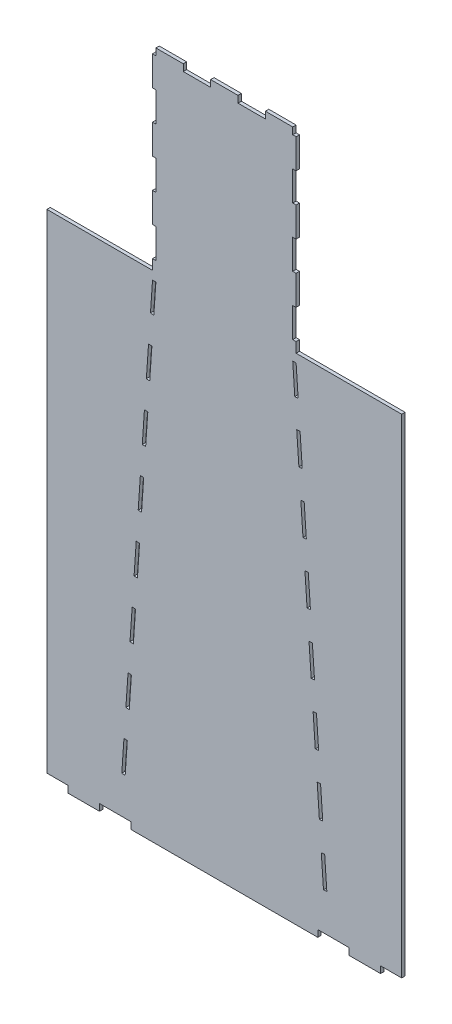
SolidWorks part; units mm, degrees
material "A-Glass Fiber"
ref_plane "Front Plane" through (0, 0, 0) normal (0, 0, 1) x (1, 0, 0)
ref_plane "Top Plane" through (0, 0, 0) normal (0, 1, 0) x (1, 0, 0)
ref_plane "Right Plane" through (0, 0, 0) normal (1, 0, 0) x (0, 0, -1)
sketch "Sketch1" plane through (0, 0, 0) normal (0, 0, 1) x (1, 0, 0)
  line L0 (-215.8818, 2072.64) -> (-215.8818, 1463.04) construction
  line L1 (308.2661, 132.944) -> (301.7555, 226.6808) construction
  line L2 (-292.1, 0) -> (292.1, 0) construction
  line L3 (-215.8818, 2072.64) -> (215.8818, 2072.64) construction
  line L4 (301.7555, 226.6808) -> (291.6378, 225.9781) construction
  line L5 (-205.7153, 2072.64) -> (-123.444, 2072.64)
  line L6 (-123.444, 2052.32) -> (-123.444, 2072.64)
  line L7 (-123.444, 2052.32) -> (-123.444, 2072.64)
  line L8 (-41.1356, 2072.64) -> (-41.1356, 2052.32)
  line L9 (-41.1356, 2072.64) -> (41.1356, 2072.64)
  line L10 (0, 2072.64) -> (0, 0) construction
  line L11 (291.6378, 225.9781) -> (298.1484, 132.2412) construction
  line L12 (-280.9748, 20.32) -> (280.9748, 20.32)
  line L13 (298.1484, 132.2412) -> (308.2661, 132.944) construction
  line L14 (289.4357, 404.0535) -> (279.318, 403.3508) construction
  line L15 (279.318, 403.3508) -> (285.8305, 309.5874) construction
  line L16 (285.8305, 309.5874) -> (295.9482, 310.2901) construction
  line L17 (-205.7153, 2072.64) -> (-123.444, 2072.64) construction
  line L18 (-205.7153, 2072.64) -> (-205.7153, 1963.42)
  line L19 (-205.7153, 1963.42) -> (-215.8818, 1963.42)
  line L20 (-215.8818, 2052.32) -> (-215.8818, 1963.42)
  line L21 (-205.7153, 1963.42) -> (-215.8818, 1963.42)
  line L23 (-205.7153, 1874.52) -> (-215.8818, 1874.52)
  line L26 (295.9482, 310.2901) -> (289.4357, 404.0535) construction
  line L28 (205.7153, 1696.72) -> (215.8753, 1696.72)
  line L29 (215.8753, 1696.72) -> (215.8753, 1607.82)
  line L30 (205.7153, 1696.72) -> (215.8753, 1696.72)
  line L31 (205.7153, 1607.82) -> (215.8753, 1607.82)
  line L32 (283.6303, 487.6362) -> (277.1159, 581.4262) construction
  line L33 (205.7153, 1607.82) -> (215.8753, 1607.82)
  line L34 (-205.7153, 1518.92) -> (215.8818, 1518.92)
  line L35 (205.7153, 1785.62) -> (215.8818, 1785.62)
  line L36 (-205.7153, 1518.92) -> (215.8818, 1518.92)
  line L37 (-215.8818, 1463.04) -> (-205.7153, 1463.04)
  line L38 (277.1159, 581.4262) -> (266.9983, 580.7234) construction
  line L39 (-215.8818, 1463.04) -> (-205.7153, 1463.04) construction
  line L40 (-205.7153, 1463.04) -> (-205.7153, 2072.64)
  line L41 (266.9983, 580.7234) -> (273.5126, 486.9335) construction
  line L42 (273.5126, 486.9335) -> (283.6303, 487.6362) construction
  line L43 (264.7962, 758.7989) -> (254.6785, 758.0961) construction
  line L44 (215.8818, 1463.04) -> (205.7153, 1463.04) construction
  line L45 (254.6785, 758.0961) -> (261.1947, 664.2796) construction
  line L46 (261.1947, 664.2796) -> (271.3124, 664.9824) construction
  line L47 (271.3124, 664.9824) -> (264.7962, 758.7989) construction
  line L48 (252.4764, 936.1715) -> (242.3588, 935.4688) construction
  line L50 (242.3588, 935.4688) -> (248.8768, 841.6258) construction
  line L52 (248.8768, 841.6258) -> (258.9945, 842.3285) construction
  line L53 (258.9945, 842.3285) -> (252.4764, 936.1715) construction
  line L54 (240.1567, 1113.5442) -> (230.039, 1112.8414) construction
  line L55 (230.039, 1112.8414) -> (236.5589, 1018.9719) construction
  line L56 (236.5589, 1018.9719) -> (246.6766, 1019.6747) construction
  line L57 (246.6766, 1019.6747) -> (240.1567, 1113.5442) construction
  line L58 (227.8369, 1290.9169) -> (217.7192, 1290.2141) construction
  line L59 (217.7192, 1290.2141) -> (224.241, 1196.3181) construction
  line L60 (224.241, 1196.3181) -> (234.3587, 1197.0208) construction
  line L61 (234.3587, 1197.0208) -> (227.8369, 1290.9169) construction
  line L62 (205.7153, 1463.04) -> (211.9231, 1373.6642) construction
  line L63 (211.9231, 1373.6642) -> (222.0407, 1374.3669) construction
  line L64 (222.0407, 1374.3669) -> (215.8818, 1463.04) construction
  line L65 (215.8818, 1463.04) -> (205.7153, 1463.04) construction
  line L66 (-211.9231, 1373.6642) -> (-205.7153, 1463.04) construction
  line L67 (-280.9748, 20.32) -> (-291.0414, 20.32)
  line L68 (-205.7153, 1463.04) -> (-215.8818, 1463.04) construction
  line L69 (-215.8818, 1463.04) -> (-222.0407, 1374.3669) construction
  line L70 (-280.9748, 20.32) -> (-280.9748, 0)
  line L71 (-222.0407, 1374.3669) -> (-211.9231, 1373.6642) construction
  line L72 (-217.7192, 1290.2141) -> (-227.8369, 1290.9169) construction
  line L73 (-227.8369, 1290.9169) -> (-234.3587, 1197.0208) construction
  line L74 (-234.3587, 1197.0208) -> (-224.241, 1196.3181) construction
  line L75 (-224.241, 1196.3181) -> (-217.7192, 1290.2141) construction
  line L76 (-230.039, 1112.8414) -> (-240.1567, 1113.5442) construction
  line L77 (-240.1567, 1113.5442) -> (-246.6766, 1019.6747) construction
  line L78 (-168.402, 20.32) -> (-168.402, 0)
  line L79 (-246.6766, 1019.6747) -> (-236.5589, 1018.9719) construction
  line L80 (-236.5589, 1018.9719) -> (-230.039, 1112.8414) construction
  line L81 (-242.3588, 935.4688) -> (-252.4764, 936.1715) construction
  line L82 (205.7153, 2072.64) -> (123.444, 2072.64) construction
  line L83 (-168.402, 20.32) -> (-168.402, 0)
  line L86 (-205.7153, 2052.32) -> (-215.8818, 2052.32)
  line L87 (292.1, 0) -> (-292.1, 0)
  line L88 (-280.9748, 0) -> (-168.402, 0)
  line L89 (-252.4764, 936.1715) -> (-258.9945, 842.3285) construction
  line L90 (215.8818, 2072.64) -> (215.8818, 1463.04) construction
  line L91 (-215.8818, 2052.32) -> (-205.7153, 2052.32)
  line L92 (215.8818, 2052.32) -> (205.7153, 2052.32)
  line L93 (280.9748, 0) -> (168.402, 0)
  line L94 (205.7153, 2052.32) -> (-215.8818, 2052.32)
  line L97 (168.402, 20.32) -> (168.402, 0)
  line L98 (-258.9945, 842.3285) -> (-248.8768, 841.6258) construction
  line L99 (-248.8768, 841.6258) -> (-242.3588, 935.4688) construction
  line L100 (168.402, 20.32) -> (168.402, 0)
  line L101 (-254.6785, 758.0961) -> (-264.7962, 758.7989) construction
  line L102 (-264.7962, 758.7989) -> (-271.3124, 664.9824) construction
  line L104 (-271.3124, 664.9824) -> (-261.1947, 664.2796) construction
  line L105 (-261.1947, 664.2796) -> (-254.6785, 758.0961) construction
  line L106 (-277.1159, 581.4262) -> (-283.6303, 487.6362) construction
  line L107 (-283.6303, 487.6362) -> (-273.5126, 486.9335) construction
  line L108 (280.9748, 20.32) -> (280.9748, 0)
  line L109 (-273.5126, 486.9335) -> (-266.9983, 580.7234) construction
  line L110 (280.9748, 20.32) -> (291.0414, 20.32)
  line L111 (-266.9983, 580.7234) -> (-277.1159, 581.4262) construction
  line L112 (-279.318, 403.3508) -> (-289.4357, 404.0535) construction
  line L113 (-289.4357, 404.0535) -> (-295.9482, 310.2901) construction
  line L114 (-295.9482, 310.2901) -> (-285.8305, 309.5874) construction
  line L116 (-285.8305, 309.5874) -> (-279.318, 403.3508) construction
  line L117 (-301.7555, 226.6808) -> (-308.2661, 132.944) construction
  line L120 (-308.2661, 132.944) -> (-298.1484, 132.2412) construction
  line L121 (-298.1484, 132.2412) -> (-291.6378, 225.9781) construction
  line L124 (-291.6378, 225.9781) -> (-301.7555, 226.6808) construction
  line L125 (308.2661, 132.944) -> (301.7555, 226.6808)
  line L127 (301.7555, 226.6808) -> (291.6378, 225.9781)
  line L128 (205.7153, 1463.04) -> (205.7153, 2072.64)
  line L129 (215.8818, 1463.04) -> (205.7153, 1463.04)
  line L130 (205.7153, 1518.92) -> (-215.8818, 1518.92)
  line L131 (-205.7153, 1518.92) -> (-215.8818, 1518.92)
  line L132 (205.7153, 1518.92) -> (-215.8818, 1518.92)
  line L133 (-205.7153, 1607.82) -> (-215.8753, 1607.82)
  line L134 (291.6378, 225.9781) -> (298.1484, 132.2412)
  line L135 (-205.7153, 1607.82) -> (-215.8753, 1607.82)
  line L136 (-205.7153, 1696.72) -> (-215.8753, 1696.72)
  line L137 (-215.8753, 1696.72) -> (-215.8753, 1607.82)
  line L138 (-205.7153, 1696.72) -> (-215.8753, 1696.72)
  line L143 (-215.8818, 1518.92) -> (-215.8818, 1463.04)
  line L145 (205.7153, 1963.42) -> (215.8818, 1963.42)
  line L146 (215.8818, 2052.32) -> (215.8818, 1963.42)
  line L147 (205.7153, 1963.42) -> (215.8818, 1963.42)
  line L148 (205.7153, 2072.64) -> (205.7153, 1963.42)
  line L149 (41.1356, 2072.64) -> (41.1356, 2052.32)
  line L150 (123.444, 2052.32) -> (123.444, 2072.64)
  line L151 (123.444, 2052.32) -> (123.444, 2072.64)
  line L152 (205.7153, 2072.64) -> (123.444, 2072.64)
  line L153 (298.1484, 132.2412) -> (308.2661, 132.944)
  line L154 (205.7153, 1518.92) -> (215.8818, 1518.92)
  line L155 (215.8818, 1518.92) -> (215.8818, 1463.04)
  line L156 (-205.7153, 1785.62) -> (-215.8818, 1785.62)
  line L165 (-215.8818, 1874.52) -> (-215.8818, 1785.62)
  line L166 (215.8818, 1874.52) -> (215.8818, 1785.62)
  line L167 (205.7153, 1874.52) -> (215.8818, 1874.52)
  line L168 (215.8818, 1488.44) -> (469.8818, 1488.44)
  line L169 (-55.8292, 20.32) -> (55.8292, 20.32)
  line L170 (-55.8292, 20.32) -> (-55.8292, 0)
  line L171 (-55.8292, 0) -> (55.8292, 0)
  line L172 (55.8292, 20.32) -> (55.8292, 0)
  line L173 (469.8818, 1488.44) -> (469.8818, 20.32)
  line L174 (469.8818, 20.32) -> (291.0414, 20.32)
  line L175 (-215.8818, 1488.44) -> (-469.8818, 1488.44)
  line L176 (-469.8818, 1488.44) -> (-469.8818, 20.32)
  line L177 (-291.0414, 20.32) -> (-469.8818, 20.32)
  line L178 (289.4357, 404.0535) -> (279.318, 403.3508)
  line L179 (279.318, 403.3508) -> (285.8305, 309.5874)
  line L180 (-375.4283, 0) -> (-280.9748, 0) construction
  line L181 (-469.8818, 20.32) -> (-375.4283, 20.32)
  line L182 (-469.8818, 20.32) -> (-469.8818, 0)
  line L183 (-469.8818, 0) -> (-375.4283, 0)
  line L184 (-375.4283, 20.32) -> (-375.4283, 0)
  line L185 (280.9748, 0) -> (375.4283, 0) construction
  line L186 (-375.4283, 0) -> (-280.9748, 0)
  line L187 (-375.4283, 0) -> (-375.4283, 20.32)
  line L188 (-375.4283, 20.32) -> (-280.9748, 20.32)
  line L189 (-280.9748, 0) -> (-280.9748, 20.32)
  line L190 (469.8818, 20.32) -> (375.4283, 20.32)
  line L191 (469.8818, 20.32) -> (469.8818, 0)
  line L192 (469.8818, 0) -> (375.4283, 0)
  line L193 (375.4283, 20.32) -> (375.4283, 0)
  line L194 (285.8305, 309.5874) -> (295.9482, 310.2901)
  line L195 (375.4283, 0) -> (280.9748, 0)
  line L196 (375.4283, 0) -> (375.4283, 20.32)
  line L197 (375.4283, 20.32) -> (280.9748, 20.32)
  line L198 (280.9748, 0) -> (280.9748, 20.32)
  line L199 (295.9482, 310.2901) -> (289.4357, 404.0535)
  line L200 (283.6303, 487.6362) -> (277.1159, 581.4262)
  line L201 (277.1159, 581.4262) -> (266.9983, 580.7234)
  line L202 (266.9983, 580.7234) -> (273.5126, 486.9335)
  line L203 (273.5126, 486.9335) -> (283.6303, 487.6362)
  line L204 (264.7962, 758.7989) -> (254.6785, 758.0961)
  line L205 (254.6785, 758.0961) -> (261.1947, 664.2796)
  line L206 (261.1947, 664.2796) -> (271.3124, 664.9824)
  line L207 (271.3124, 664.9824) -> (264.7962, 758.7989)
  line L208 (252.4764, 936.1715) -> (242.3588, 935.4688)
  line L209 (242.3588, 935.4688) -> (248.8768, 841.6258)
  line L210 (248.8768, 841.6258) -> (258.9945, 842.3285)
  line L211 (258.9945, 842.3285) -> (252.4764, 936.1715)
  line L212 (240.1567, 1113.5442) -> (230.039, 1112.8414)
  line L213 (230.039, 1112.8414) -> (236.5589, 1018.9719)
  line L214 (236.5589, 1018.9719) -> (246.6766, 1019.6747)
  line L215 (246.6766, 1019.6747) -> (240.1567, 1113.5442)
  line L216 (227.8369, 1290.9169) -> (217.7192, 1290.2141)
  line L217 (217.7192, 1290.2141) -> (224.241, 1196.3181)
  line L218 (224.241, 1196.3181) -> (234.3587, 1197.0208)
  line L219 (234.3587, 1197.0208) -> (227.8369, 1290.9169)
  line L220 (205.7153, 1463.04) -> (211.9231, 1373.6642)
  line L221 (211.9231, 1373.6642) -> (222.0407, 1374.3669)
  line L222 (222.0407, 1374.3669) -> (215.8818, 1463.04)
  line L223 (215.8818, 1463.04) -> (205.7153, 1463.04)
  line L224 (-211.9231, 1373.6642) -> (-205.7153, 1463.04)
  line L225 (-205.7153, 1463.04) -> (-215.8818, 1463.04)
  line L226 (-215.8818, 1463.04) -> (-222.0407, 1374.3669)
  line L227 (-222.0407, 1374.3669) -> (-211.9231, 1373.6642)
  line L228 (-217.7192, 1290.2141) -> (-227.8369, 1290.9169)
  line L229 (-227.8369, 1290.9169) -> (-234.3587, 1197.0208)
  line L230 (-234.3587, 1197.0208) -> (-224.241, 1196.3181)
  line L231 (-224.241, 1196.3181) -> (-217.7192, 1290.2141)
  line L232 (-230.039, 1112.8414) -> (-240.1567, 1113.5442)
  line L233 (-240.1567, 1113.5442) -> (-246.6766, 1019.6747)
  line L234 (-246.6766, 1019.6747) -> (-236.5589, 1018.9719)
  line L235 (-236.5589, 1018.9719) -> (-230.039, 1112.8414)
  line L236 (-242.3588, 935.4688) -> (-252.4764, 936.1715)
  line L237 (-252.4764, 936.1715) -> (-258.9945, 842.3285)
  line L238 (-258.9945, 842.3285) -> (-248.8768, 841.6258)
  line L239 (-248.8768, 841.6258) -> (-242.3588, 935.4688)
  line L240 (-254.6785, 758.0961) -> (-264.7962, 758.7989)
  line L241 (-264.7962, 758.7989) -> (-271.3124, 664.9824)
  line L242 (-271.3124, 664.9824) -> (-261.1947, 664.2796)
  line L243 (-261.1947, 664.2796) -> (-254.6785, 758.0961)
  line L244 (-277.1159, 581.4262) -> (-283.6303, 487.6362)
  line L245 (-283.6303, 487.6362) -> (-273.5126, 486.9335)
  line L246 (-273.5126, 486.9335) -> (-266.9983, 580.7234)
  line L247 (-266.9983, 580.7234) -> (-277.1159, 581.4262)
  line L248 (-279.318, 403.3508) -> (-289.4357, 404.0535)
  line L249 (-289.4357, 404.0535) -> (-295.9482, 310.2901)
  line L250 (-295.9482, 310.2901) -> (-285.8305, 309.5874)
  line L251 (-285.8305, 309.5874) -> (-279.318, 403.3508)
  line L252 (-301.7555, 226.6808) -> (-308.2661, 132.944)
  line L253 (-308.2661, 132.944) -> (-298.1484, 132.2412)
  line L254 (-298.1484, 132.2412) -> (-291.6378, 225.9781)
  line L255 (-291.6378, 225.9781) -> (-301.7555, 226.6808)
  line L257 (469.8818, 1488.44) -> (533.3818, 1488.44)
  line L258 (469.8818, 1488.44) -> (469.8818, 0)
  line L259 (469.8818, 0) -> (533.3818, 0)
  line L260 (533.3818, 1488.44) -> (533.3818, 0)
  line L261 (-469.8818, 1488.44) -> (-533.3818, 1488.44)
  line L262 (-469.8818, 1488.44) -> (-469.8818, 0)
  line L263 (-469.8818, 0) -> (-533.3818, 0)
  line L264 (-533.3818, 1488.44) -> (-533.3818, 0)
  point P130 (-210.7985, 1463.04)
  point P141 (0, 20.32)
  dimension "D2" = 112.5728
  dimension "D3" = 609.6
  dimension "D4" = 2072.64
  dimension "D5" = 20.32
  dimension "D6" = 88.9
  dimension "D7" = 20.32
  dimension "D8" = 336.804
  dimension "D9" = 41.1356
  dimension "D10" = 10.1665
  dimension "D11" = 205.7153
  dimension "D12" = 10.16
  dimension "D13" = 10.16
  dimension "D14" = 88.9
  dimension "D15" = 88.9
  dimension "D16" = 88.9
  dimension "D17" = 112.5728
  dimension "D18" = 88.9
  dimension "D19" = 112.5728
  dimension "D20" = 88.9
  dimension "D21" = 20.32
  dimension "D22" = 254
  dimension "D23" = 254
  dimension "D24" = 25.4
  dimension "D25" = 25.4
  dimension "D26" = 63.5
  dimension "D27" = 63.5
extrude "Boss-Extrude1" add sketch "Sketch1" along normal blind 10.16
sketch "Sketch5" plane through (0, 0, 10.16) normal (0, 0, 1) x (1, 0, 0)
  line L1 (-533.3818, 0) -> (-469.8818, 0)
  line L2 (-533.3818, 0) -> (-533.3818, 20.32)
  line L3 (-533.3818, 20.32) -> (-469.8818, 20.32)
  line L4 (-469.8818, 0) -> (-469.8818, 20.32)
  line L5 (533.3818, 0) -> (469.8818, 0)
  line L6 (533.3818, 0) -> (533.3818, 20.32)
  line L7 (533.3818, 20.32) -> (469.8818, 20.32)
  line L8 (469.8818, 0) -> (469.8818, 20.32)
extrude "Cut-Extrude1" cut sketch "Sketch5" against normal through all
